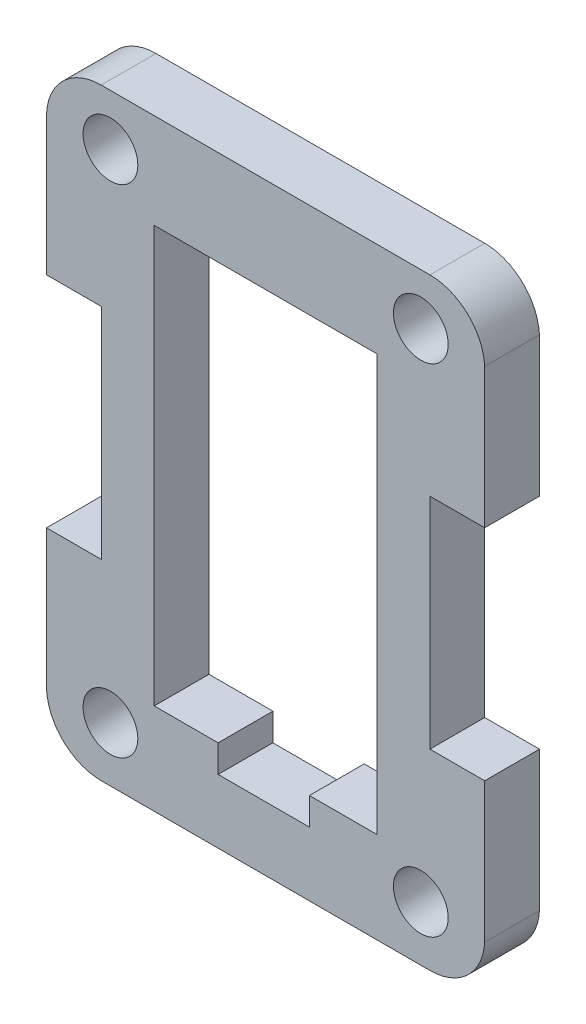
SolidWorks part; units mm, degrees
ref_plane "Front Plane" through (0, 0, 0) normal (0, 0, 1) x (1, 0, 0)
ref_plane "Top Plane" through (0, 0, 0) normal (0, 1, 0) x (1, 0, 0)
ref_plane "Right Plane" through (0, 0, 0) normal (1, 0, 0) x (0, 0, -1)
sketch "Model" plane through (0, 0, 0) normal (0, 0, 1) x (1, 0, 0)
  line L0 (41.9999, 34) -> (41.9999, 26.3436)
  line L1 (44.9999, 34) -> (41.9999, 34)
  line L2 (44.9999, 46) -> (44.9999, 34)
  line L3 (41.9999, 46) -> (44.9999, 46)
  line L4 (41.9999, 53.658) -> (41.9999, 46)
  line L5 (44.9959, 23.5) -> (62.9999, 23.5)
  line L6 (65.9999, 46) -> (65.9999, 53.6572)
  line L7 (44.9938, 56.5) -> (63.002, 56.5)
  line L8 (65.9999, 34) -> (65.9999, 26.3428)
  line L9 (47.8979, 51.3) -> (47.8979, 28.5)
  line L10 (60.0979, 51.3) -> (47.8979, 51.3)
  line L11 (60.0979, 28.5) -> (60.0979, 51.3)
  line L12 (56.3979, 28.5) -> (60.0979, 28.5)
  line L13 (56.3979, 27) -> (56.3979, 28.5)
  line L14 (51.3979, 27) -> (56.3979, 27)
  line L15 (51.3979, 28.5) -> (51.3979, 27)
  line L16 (47.8979, 28.5) -> (51.3979, 28.5)
  line L17 (62.9999, 46) -> (65.9999, 46)
  line L18 (62.9999, 34) -> (62.9999, 46)
  line L19 (65.9999, 34) -> (62.9999, 34)
  line L20 (53.9979, 56.5) -> (53.9979, 23.5) construction
  circle A0 centre (45.4999, 53.7001) radius 1.5
  circle A1 centre (62.4999, 53.7001) radius 1.5
  circle A2 centre (45.4999, 26.5) radius 1.5
  circle A3 centre (62.4999, 26.5) radius 1.5
  arc A4 (41.9999, 26.3436) -> (44.9959, 23.5) centre (44.9957, 26.4999) ccw
  arc A5 (44.9938, 56.5) -> (41.9999, 53.658) centre (44.9956, 53.5001) ccw
  arc A6 (62.9999, 23.5) -> (65.9999, 26.3428) centre (63.0041, 26.4999) ccw
  arc A7 (65.9999, 53.6572) -> (63.002, 56.5) centre (63.0041, 53.5001) ccw
  dimension "D5" = 17
  dimension "D6" = 17
  dimension "D7" = 27.2001
  dimension "D8" = 3.5
  dimension "D9" = 3.5
  dimension "D1" = 3
  dimension "D2" = 3
  dimension "D3" = 22.8
  dimension "D4" = 12.2
  dimension "D10" = 3.5
  dimension "D11" = 1.5
  dimension "D12" = 10.5
  dimension "D13" = 12
  dimension "D14" = 10.5
extrude "Boss-Extrude1" add sketch "Model" along normal blind 3
